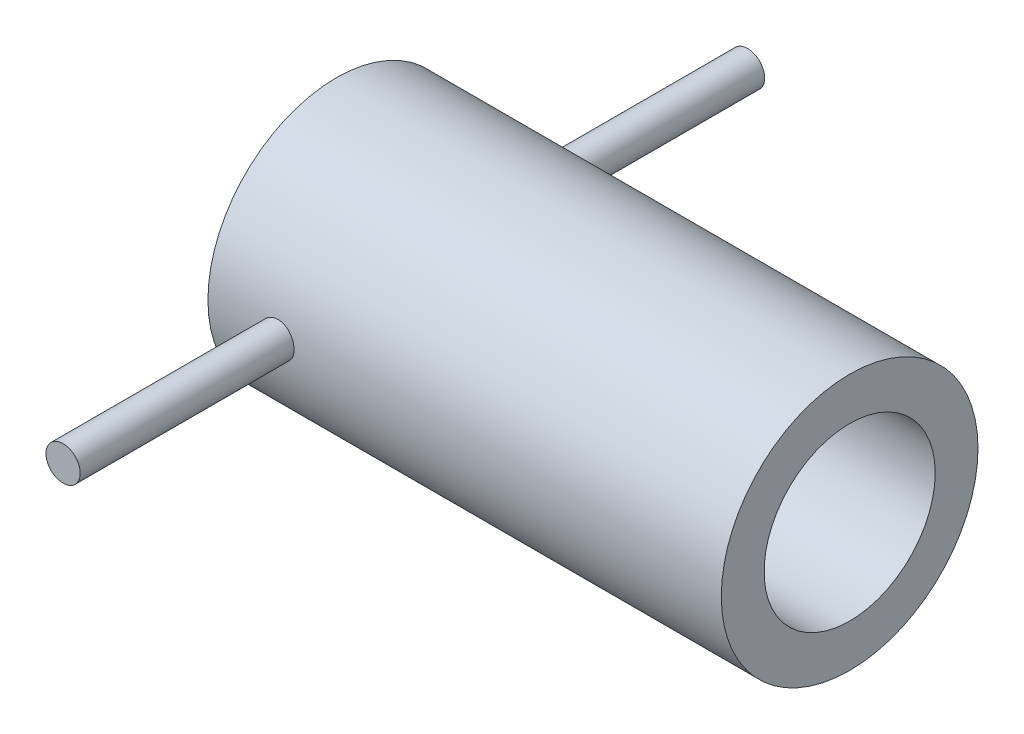
SolidWorks part; units mm, degrees
ref_plane "Front Plane" through (0, 0, 0) normal (0, 0, 1) x (1, 0, 0)
ref_plane "Top Plane" through (0, 0, 0) normal (0, 1, 0) x (1, 0, 0)
ref_plane "Right Plane" through (0, 0, 0) normal (1, 0, 0) x (0, 0, -1)
sketch "Sketch1" plane through (0, 0, 0) normal (1, 0, 0) x (0, 0, -1)
  circle A0 centre (0, 0) radius 25
  circle A1 centre (0, 0) radius 37.5
  dimension "D1" = 75
  dimension "D2" = 50
extrude "Boss-Extrude1" add sketch "Sketch1" along normal mid plane 150
sketch "Sketch2" plane through (0, 0, 0) normal (0, 0, 1) x (1, 0, 0)
  circle A0 centre (-54.8254, 0) radius 5
  dimension "D1" = 10
extrude "Boss-Extrude2" add sketch "Sketch2" along normal mid plane 200
